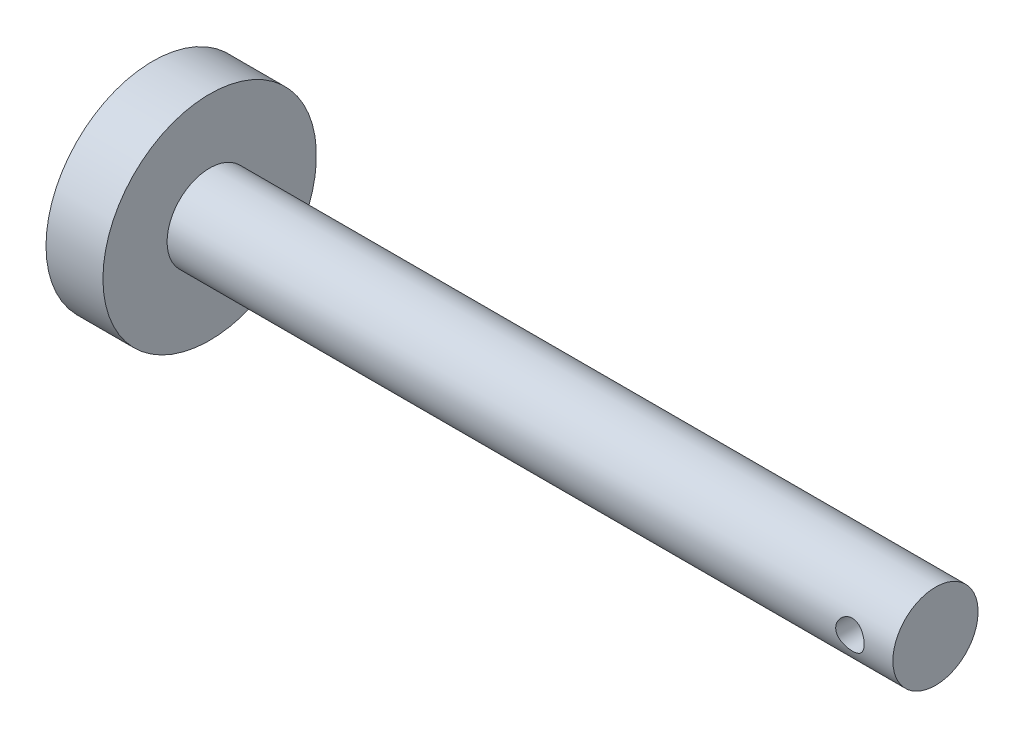
SolidWorks part; units mm, degrees
ref_plane "Front Plane" through (0, 0, 0) normal (0, 0, 1) x (1, 0, 0)
ref_plane "Top Plane" through (0, 0, 0) normal (0, 1, 0) x (1, 0, 0)
ref_plane "Right Plane" through (0, 0, 0) normal (1, 0, 0) x (0, 0, -1)
sketch "Sketch1" plane through (0, 0, 0) normal (0, 0, 1) x (1, 0, 0)
  line L0 (-16.0672, 0) -> (38.9328, 0)
  line L1 (38.9328, 0) -> (38.9328, 2.9922)
  line L2 (38.9328, 2.9922) -> (-12.0672, 2.9922)
  line L3 (-12.0672, 2.9922) -> (-12.0672, 7.5)
  line L4 (-12.0672, 7.5) -> (-16.0672, 7.5)
  line L5 (-16.0672, 7.5) -> (-16.0672, 0)
  dimension "D1" = 7.5
  dimension "D2" = 4
  dimension "D3" = 55
revolve "Revolve2" add sketch "Sketch1" angle 360 about L0
sketch "Sketch2" plane through (0, 0, 0) normal (0, 0, 1) x (1, 0, 0)
  circle A0 centre (35.9119, 0) radius 1
extrude "Cut-Extrude2" cut sketch "Sketch2" against normal through all both and the other way through all
